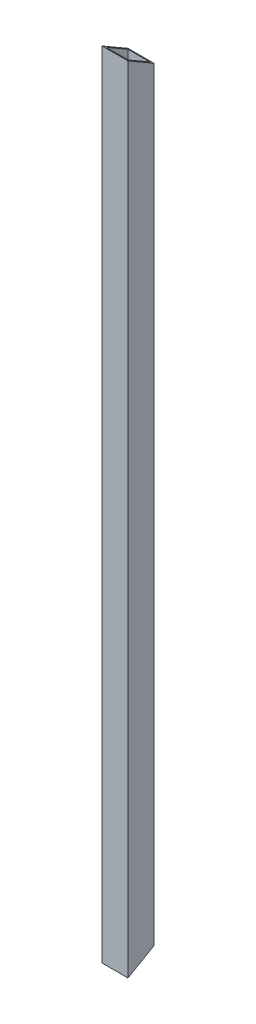
SolidWorks part; units mm, degrees
ref_plane "Front Plane" through (0, 0, 0) normal (0, 0, 1) x (1, 0, 0)
ref_plane "Top Plane" through (0, 0, 0) normal (0, 1, 0) x (1, 0, 0)
ref_plane "Right Plane" through (0, 0, 0) normal (1, 0, 0) x (0, 0, -1)
sketch "Sketch1" plane through (0, 0, 0) normal (0, 1, 0) x (1, 0, 0)
  line L0 (-6.5, 6.5) -> (6.5, 6.5)
  line L1 (-5.5, 5.5) -> (5.5, 5.5)
  line L2 (-5.5, 5.5) -> (-5.5, -5.5)
  line L3 (-5.5, -5.5) -> (5.5, -5.5)
  line L4 (5.5, 5.5) -> (5.5, -5.5)
  line L5 (-5.5, 5.5) -> (5.5, -5.5) construction
  line L6 (-5.5, -5.5) -> (5.5, 5.5) construction
  line L7 (6.5, 6.5) -> (6.5, -6.5)
  line L8 (-6.5, -6.5) -> (6.5, -6.5)
  line L9 (-6.5, 6.5) -> (-6.5, -6.5)
  point P0 (0, 0)
  dimension "D1" = 11
  dimension "D2" = 11
  dimension "D3" = 1
extrude "Boss-Extrude1" add sketch "Sketch1" along normal blind 400
sketch "Sketch2" plane through (-6.5, 0, 0) normal (-1, 0, 0) x (0, 0, 1)
  line L0 (6.5, 400) -> (-6.5, 392.4944)
  line L1 (-6.5, 400) -> (-6.5, 0) construction
extrude "Cut-Extrude1" cut sketch "Sketch2" against normal through all and the other way through all flip side to cut
sketch "Sketch3" plane through (-6.5, 0, 0) normal (-1, 0, 0) x (0, 0, 1)
  line L0 (6.5, 0) -> (-6.5, 7.5056)
  line L1 (-6.5, 392.4944) -> (-6.5, 0) construction
extrude "Cut-Extrude3" cut sketch "Sketch3" against normal through all both and the other way through all
